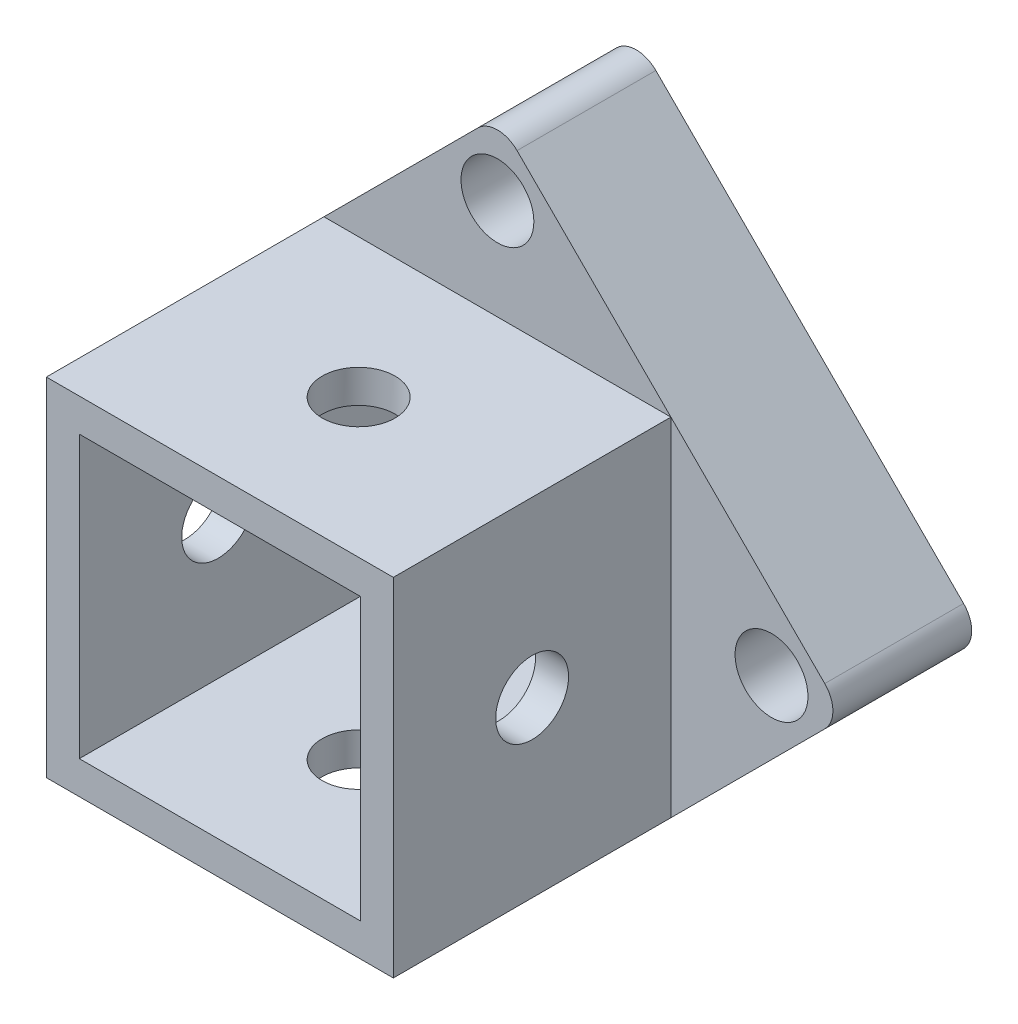
SolidWorks part; units mm, degrees
ref_plane "Front Plane" through (0, 0, 0) normal (0, 0, 1) x (1, 0, 0)
ref_plane "Top Plane" through (0, 0, 0) normal (0, 1, 0) x (1, 0, 0)
ref_plane "Right Plane" through (0, 0, 0) normal (1, 0, 0) x (0, 0, -1)
sketch "Sketch1" plane through (0, 0, 0) normal (0, 0, 1) x (1, 0, 0)
  line L1 (-10.125, -10.125) -> (10.125, -10.125)
  line L2 (-10.125, -10.125) -> (-10.125, 10.125)
  line L3 (-10.125, 10.125) -> (10.125, 10.125)
  line L4 (10.125, -10.125) -> (10.125, 10.125)
  line L5 (-10.125, -10.125) -> (10.125, 10.125) construction
  line L6 (-10.125, 10.125) -> (10.125, -10.125) construction
  line L7 (-12.5, -12.5) -> (12.5, -12.5)
  line L8 (-12.5, -12.5) -> (-12.5, 12.5)
  line L9 (-12.5, 12.5) -> (12.5, 12.5)
  line L10 (12.5, -12.5) -> (12.5, 12.5)
  line L11 (-12.5, -12.5) -> (12.5, 12.5) construction
  line L12 (-12.5, 12.5) -> (12.5, -12.5) construction
  point P0 (0, 0)
  point P5 (0, 0)
  dimension "D1" = 20.25
  dimension "D2" = 25
extrude "Boss-Extrude1" add sketch "Sketch1" along normal mid plane 10
sketch "Sketch2" plane through (0, 0, 0) normal (0, 0, 1) x (1, 0, 0)
  line L0 (-25, 0) -> (0, 25)
  line L1 (0, 25) -> (25, 0)
  line L2 (25, 0) -> (0, -25)
  line L3 (0, -25) -> (-25, 0)
  line L4 (-10.125, -10.125) -> (10.125, -10.125) construction
  line L5 (-10.125, 10.125) -> (-10.125, -10.125) construction
  line L6 (10.125, 10.125) -> (-10.125, 10.125) construction
  line L7 (10.125, -10.125) -> (10.125, 10.125) construction
  line L8 (-10.125, -10.125) -> (10.125, -10.125)
  line L9 (-10.125, 10.125) -> (-10.125, -10.125)
  line L10 (10.125, 10.125) -> (-10.125, 10.125)
  line L11 (10.125, -10.125) -> (10.125, 10.125)
  circle A0 centre (0, 0) radius 14.5 construction
  circle A1 centre (0, 19.75) radius 3.25 construction
  circle A2 centre (19.75, 0) radius 3.25 construction
  circle A3 centre (0, -19.75) radius 3.25 construction
  circle A4 centre (-19.75, 0) radius 3.25 construction
  circle A5 centre (0, 19.75) radius 2.625
  circle A6 centre (19.75, 0) radius 2.625
  circle A7 centre (0, -19.75) radius 2.625
  circle A8 centre (-19.75, 0) radius 2.625
  point P5 (0, 16.5)
  point P6 (0, 14.5)
  point P16 (0, 0)
  point P23 (-12.5, 12.5)
  point P34 (0, 0)
  dimension "D1" = 6.5
  dimension "D3" = 29
  dimension "D5" = 5.25
  dimension "D2" = 2
  dimension "D4" = 4
  dimension "D6" = 4
extrude "Boss-Extrude2" add sketch "Sketch2" along normal mid plane 10
sketch "Sketch3" plane through (0, 0, 5) normal (0, 0, 1) x (1, 0, 0)
  line L0 (25, 0) -> (0, 25) construction
  line L1 (-10.125, -10.125) -> (10.125, -10.125)
  line L2 (-10.125, -10.125) -> (-10.125, 10.125)
  line L3 (-10.125, 10.125) -> (10.125, 10.125)
  line L4 (10.125, -10.125) -> (10.125, 10.125)
  line L5 (-10.125, -10.125) -> (10.125, 10.125) construction
  line L6 (-10.125, 10.125) -> (10.125, -10.125) construction
  line L7 (-12.5, -12.5) -> (12.5, -12.5)
  line L8 (-12.5, -12.5) -> (-12.5, 12.5)
  line L9 (-12.5, 12.5) -> (12.5, 12.5)
  line L10 (12.5, -12.5) -> (12.5, 12.5)
  line L11 (-12.5, -12.5) -> (12.5, 12.5) construction
  line L12 (-12.5, 12.5) -> (12.5, -12.5) construction
  point P0 (0, 0)
  point P7 (0, 0)
extrude "Boss-Extrude3" add sketch "Sketch3" along normal blind 20
sketch "Sketch4" plane through (0, 12.5, 0) normal (0, 1, 0) x (1, 0, 0)
  line L1 (12.5, -15) -> (-12.5, -15) construction
  line L2 (12.5, -25) -> (12.5, -5) construction
  line L3 (-12.5, -25) -> (-12.5, -5) construction
  circle A0 centre (0, -15) radius 2.625
  dimension "D1" = 5.25
extrude "Cut-Extrude1" cut sketch "Sketch4" against normal through all
sketch "Sketch5" plane through (12.5, 0, 0) normal (1, 0, 0) x (0, 0, -1)
  line L0 (-15, 12.5) -> (-15, -12.5) construction
  line L1 (-25, 12.5) -> (-5, 12.5) construction
  line L2 (-25, -12.5) -> (-5, -12.5) construction
  circle A0 centre (-15, 0) radius 2.625
  dimension "D1" = 5.25
extrude "Cut-Extrude2" cut sketch "Sketch5" against normal through all
fillet "Fillet1" radius 2 4 edges at (0, -25, 0) (25, 0, 0) (0, 25, 0) (-25, 0, 0)
